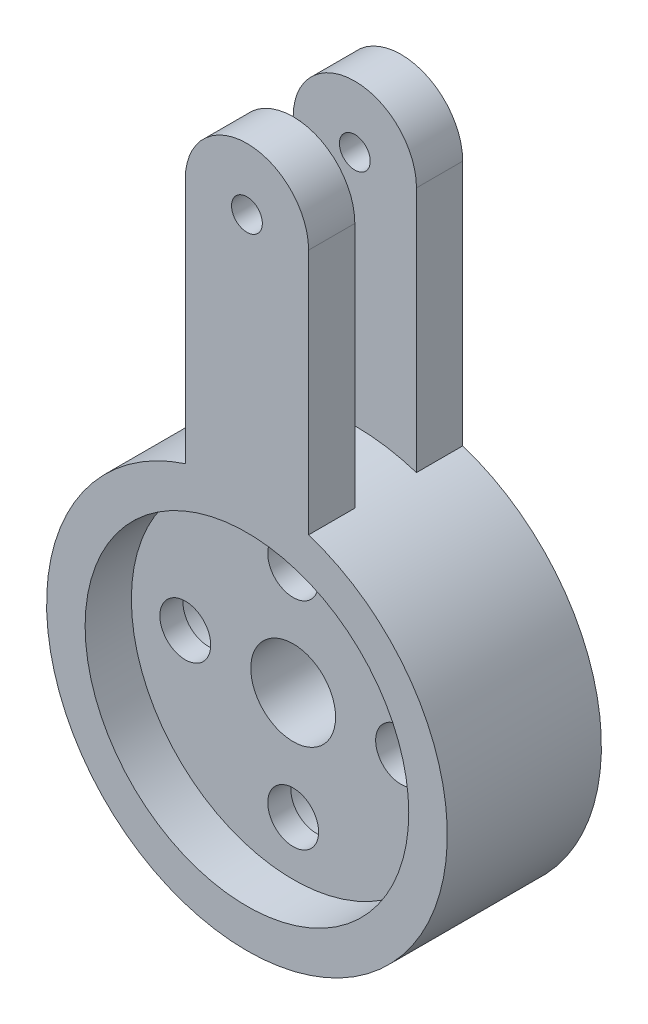
SolidWorks part; units mm, degrees
ref_plane "Plan de face" through (0, 0, 0) normal (0, 0, 1) x (1, 0, 0)
ref_plane "Plan de dessus" through (0, 0, 0) normal (0, 1, 0) x (1, 0, 0)
ref_plane "Plan de droite" through (0, 0, 0) normal (1, 0, 0) x (0, 0, -1)
sketch "Esquisse1" plane through (0, 0, 0) normal (0, 0, 1) x (1, 0, 0)
  line L0 (-7, 0) -> (0, 0) construction
  circle A0 centre (0, 0) radius 13
  circle A1 centre (0, 0) radius 2.75
  circle A2 centre (-7, 0) radius 1.65
  circle A3 centre (0, 7) radius 1.65
  circle A4 centre (7, 0) radius 1.65
  circle A5 centre (0, -7) radius 1.65
  point P15 (0, 0)
  dimension "D1" = 26
  dimension "D2" = 5.5
  dimension "D3" = 3.3
  dimension "D4" = 7
  dimension "D5" = 4
extrude "Boss.-Extru.1" add sketch "Esquisse1" along normal blind 10
sketch "Esquisse2" plane through (0, 0, 10) normal (0, 0, 1) x (1, 0, 0)
  circle A0 centre (0, 0) radius 10.5
  dimension "D1" = 21
extrude "Enlèv. mat.-Extru.1" cut sketch "Esquisse2" against normal blind 3
sketch "Esquisse3" plane through (0, 0, 0) normal (0, 0, -1) x (-1, 0, 0)
  circle A0 centre (-7, 0) radius 2.75
  circle A1 centre (0, 7) radius 2.75
  circle A2 centre (7, 0) radius 2.75
  circle A3 centre (0, -7) radius 2.75
  dimension "D1" = 5.5
extrude "Enlèv. mat.-Extru.2" cut sketch "Esquisse3" against normal blind 5.5
sketch "Esquisse4" plane through (0, 0, 0) normal (0, 0, -1) x (-1, 0, 0)
  line L0 (-4, 28.3693) -> (4, 28.3693) construction
  line L1 (-4, 12.3693) -> (4, 12.3693) construction
  line L2 (-4, 12.3693) -> (-4, 32.3693) construction
  line L3 (-4, 32.3693) -> (4, 32.3693) construction
  line L4 (4, 12.3693) -> (4, 32.3693) construction
  line L5 (-4, 28.3693) -> (-4, 12.3693)
  line L6 (4, 28.3693) -> (4, 12.3693)
  arc A0 (-4, 12.3693) -> (4, 12.3693) centre (0, 0) cw
  circle A1 centre (0, 0) radius 13 construction
  arc A2 (-4, 28.3693) -> (4, 28.3693) centre (0, 28.3693) cw
  circle A3 centre (0, 28.3693) radius 1
  dimension "D3" = 2
  dimension "D1" = 8
  dimension "D2" = 20
extrude "Boss.-Extru.2" add sketch "Esquisse4" against normal blind 3
ref_plane "Plan1" through (0, 0, 5) normal (0, 0, 1) x (1, 0, 0)
mirror "Symétrie1" about plane through (0, 0, 5) normal (0, 0, 1) of "Boss.-Extru.2"
